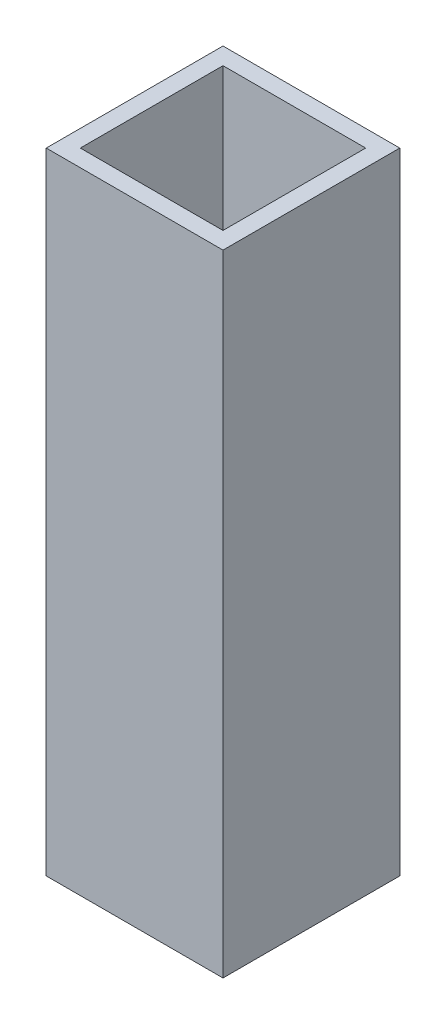
SolidWorks part; units mm, degrees
ref_plane "Front Plane" through (0, 0, 0) normal (0, 0, 1) x (1, 0, 0)
ref_plane "Top Plane" through (0, 0, 0) normal (0, 1, 0) x (1, 0, 0)
ref_plane "Right Plane" through (0, 0, 0) normal (1, 0, 0) x (0, 0, -1)
sketch "Sketch1" plane through (0, 0, 0) normal (0, 1, 0) x (1, 0, 0)
  line L1 (-6.225, -6.225) -> (6.225, -6.225)
  line L2 (-6.225, -6.225) -> (-6.225, 6.225)
  line L3 (-6.225, 6.225) -> (6.225, 6.225)
  line L4 (6.225, -6.225) -> (6.225, 6.225)
  line L5 (-6.225, -6.225) -> (6.225, 6.225) construction
  line L6 (-6.225, 6.225) -> (6.225, -6.225) construction
  point P0 (0, 0)
  dimension "D1" = 12.45
extrude "Boss-Extrude1" add sketch "Sketch1" along normal blind 44.4
shell "Shell1" thickness 1.2
sketch "Sketch2" plane through (-6.225, 0, 0) normal (-1, 0, 0) x (0, 0, 1)
  line L0 (0, 44.4) -> (0, 0) construction
  line L1 (-6.225, 44.4) -> (6.225, 44.4) construction
  line L2 (-6.225, 22.2) -> (6.225, 22.2) construction
  line L3 (-6.225, 44.4) -> (-6.225, 0) construction
  line L4 (6.225, 44.4) -> (6.225, 0) construction
  circle A0 centre (0, 22.2) radius 4.25
